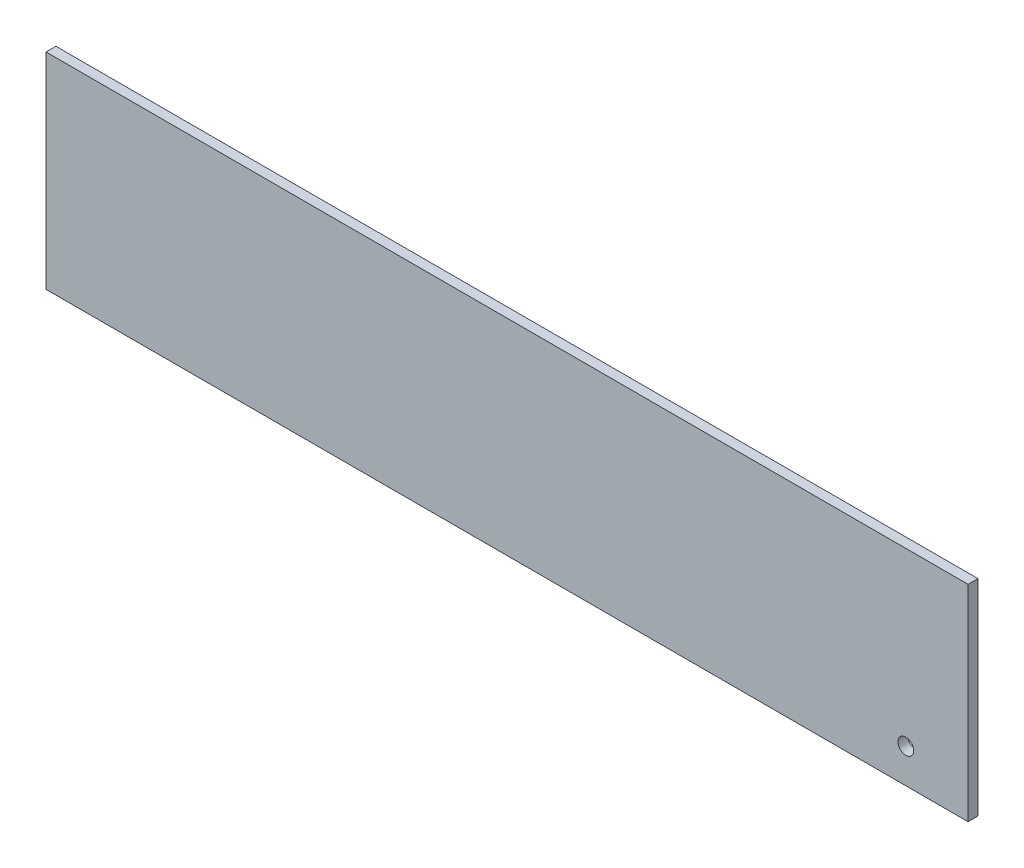
SolidWorks part; units mm, degrees
ref_plane "Front Plane" through (0, 0, 0) normal (0, 0, 1) x (1, 0, 0)
ref_plane "Top Plane" through (0, 0, 0) normal (0, 1, 0) x (1, 0, 0)
ref_plane "Right Plane" through (0, 0, 0) normal (1, 0, 0) x (0, 0, -1)
sketch "Sketch1" plane through (0, 0, 0) normal (0, 0, 1) x (1, 0, 0)
  line L1 (0, 0) -> (592, 0)
  line L2 (0, 0) -> (0, 132)
  line L3 (0, 132) -> (592, 132)
  line L4 (592, 0) -> (592, 132)
  circle A0 centre (552, 22) radius 5.05
  dimension "D3" = 10.1
  dimension "D1" = 132
  dimension "D2" = 592
  dimension "D4" = 22
  dimension "D5" = 40
extrude "Boss-Extrude1" add sketch "Sketch1" along normal blind 6.35
